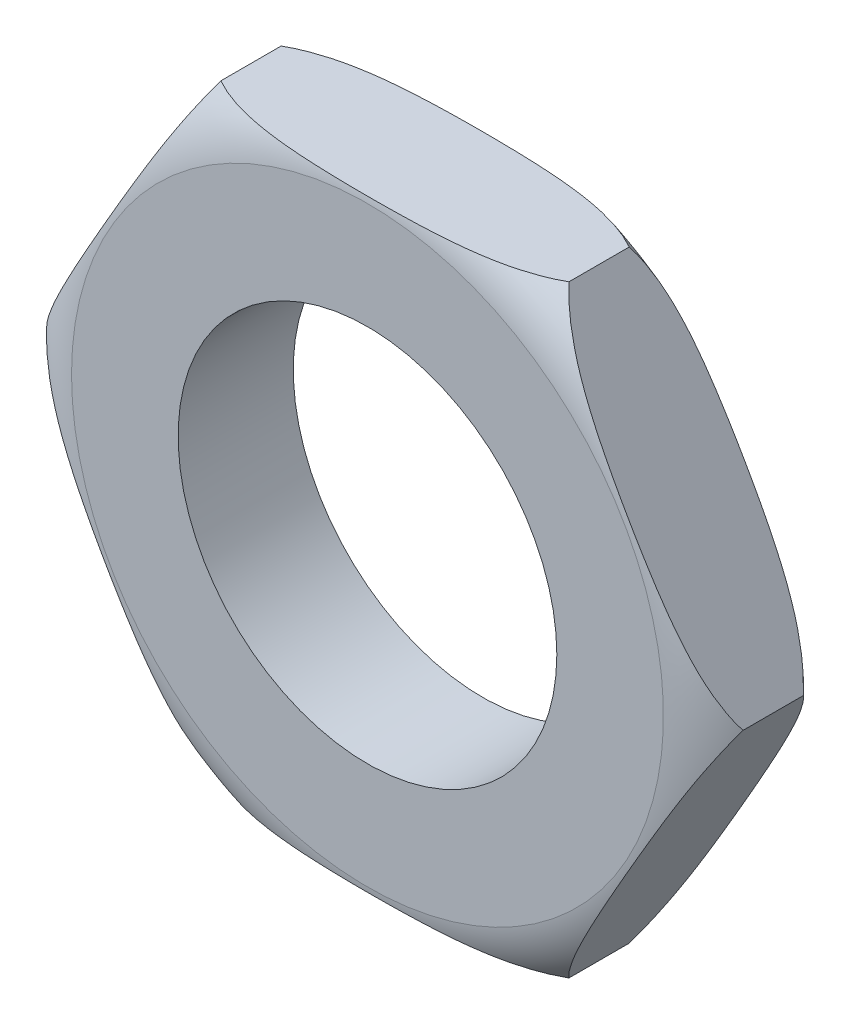
SolidWorks part; units mm, degrees
material "Plain Carbon Steel"
ref_plane "Front Plane" through (0, 0, 0) normal (0, 0, 1) x (1, 0, 0)
ref_plane "Top Plane" through (0, 0, 0) normal (0, 1, 0) x (1, 0, 0)
ref_plane "Right Plane" through (0, 0, 0) normal (1, 0, 0) x (0, 0, -1)
sketch "Sketch2" plane through (0, 0, 0) normal (0, 0, 1) x (1, 0, 0)
  line L0 (-6.3509, 0) -> (6.3509, 0) construction
  line L1 (-3.1754, -5.5) -> (3.1754, -5.5)
  line L2 (3.1754, -5.5) -> (6.3509, 0)
  line L3 (6.3509, 0) -> (3.1754, 5.5)
  line L4 (3.1754, 5.5) -> (-3.1754, 5.5)
  line L5 (-3.1754, 5.5) -> (-6.3509, 0)
  line L6 (-6.3509, 0) -> (-3.1754, -5.5)
  circle A0 centre (0, 0) radius 5.5 construction
  dimension "D1" = 11
extrude "Boss-Extrude1" add sketch "Sketch2" along normal mid plane 2.1
hole_wizard "5/16-24 Tapped Hole1" positions "Sketch3" profile "Sketch5" tap size "5/16-24" standard "ANSI Inch" end condition through all
sketch "Sketch3" plane through (0, 0, 1.05) normal (0, 0, 1) x (1, 0, 0)
  point P0 (0, 0)
sketch "Sketch5" plane through (0, 0, 1.05) normal (1, 0, 0) x (0, -1, 0)
  line L0 (0, 0) -> (0, 2.1)
  line L1 (0, 2.1) -> (3.4544, 2.1)
  line L2 (3.4544, 2.1) -> (3.4544, 0)
  line L5 (3.4544, 0) -> (0, 0)
  line L11 (0, -6.35) -> (0, 107.95) construction
  dimension "Thru Tap Drill Dia." = 6.9088
  dimension "Thru Tap Drill Depth" = 2.1
cosmetic thread "Hole Thread1" parameters "D2"=7.9375
sketch "Sketch7" plane through (0, 0, 0) normal (0, 1, 0) x (1, 0, 0)
  line L0 (-6.3509, -0.55) -> (-6.3509, -1.05)
  line L1 (-6.3509, -1.05) -> (-5.4, -1.05)
  line L2 (0, 0) -> (0, -2.9107) construction
  line L3 (0, 1.05) -> (0, -1.05) construction
  arc A0 (-6.3509, -0.55) -> (-5.4, -1.05) centre (-5.2236, 0.4396) ccw
  dimension "D3" = 1.5
  dimension "D1" = 10.8
  dimension "D2" = 0.5
revolve "Cut-Revolve2" cut sketch "Sketch7" angle 360 about L2
mirror "Mirror1" about plane through (0, 0, 0) normal (0, 0, 1) of "Cut-Revolve2"
